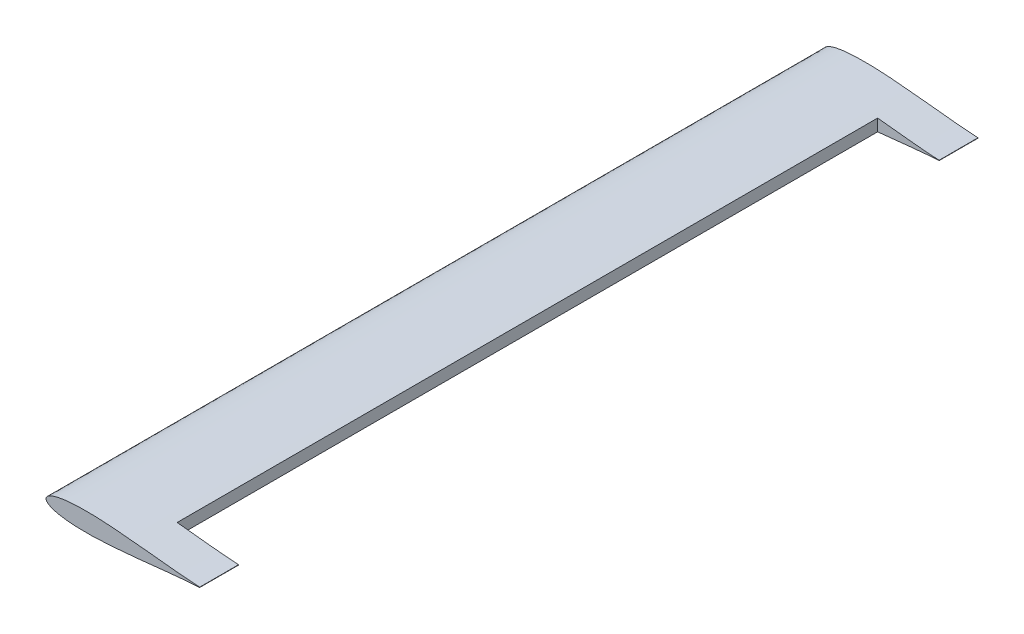
SolidWorks part; units mm, degrees
other "Markup1"
sketch "Sketch3" plane through (-0.0553, -7.355, 609.6) normal (0, 0, 1) x (1, 0, 0)
ref_plane "Front Plane" through (0, 0, 0) normal (0, 0, 1) x (1, 0, 0)
ref_plane "Top Plane" through (0, 0, 0) normal (0, 1, 0) x (1, 0, 0)
ref_plane "Right Plane" through (0, 0, 0) normal (1, 0, 0) x (0, 0, -1)
curve "Curve1"
  spline degree 3 poles (25.3337, -0.0003, 0) (25.4166, 0, 0) (25.3337, 0.0003, 0) (25.2654, 0.0018, 0) (25.098, 0.0055, 0) (24.8899, 0.0127, 0) (24.614, 0.0243, 0) (24.2833, 0.0411, 0) (23.8951, 0.064, 0) (23.4526, 0.0935, 0) (22.9577, 0.1302, 0) (22.4128, 0.1742, 0) (21.8206, 0.2257, 0) (21.184, 0.2845, 0) (20.5061, 0.3502, 0) (19.7901, 0.4224, 0) (19.0396, 0.5004, 0) (18.2582, 0.5832, 0) (17.4498, 0.6697, 0) (16.6182, 0.7589, 0) (15.7675, 0.8494, 0) (14.9019, 0.9396, 0) (14.0255, 1.0282, 0) (13.1427, 1.1135, 0) (12.2578, 1.1941, 0) (11.3749, 1.2683, 0) (10.4986, 1.3345, 0) (9.6329, 1.3915, 0) (8.7821, 1.4377, 0) (7.9504, 1.4721, 0) (7.1418, 1.4935, 0) (6.3603, 1.501, 0) (5.6096, 1.4941, 0) (4.8934, 1.4721, 0) (4.2152, 1.4349, 0) (3.5783, 1.3824, 0) (2.9857, 1.3149, 0) (2.4403, 1.233, 0) (1.9447, 1.1371, 0) (1.5013, 1.0283, 0) (1.1121, 0.9078, 0) (0.7787, 0.7769, 0) (0.5025, 0.6369, 0) (0.2843, 0.4891, 0) (0.1244, 0.334, 0) (0.024, 0.1711, 0) (-0.0113, 0, 0) (0.024, -0.1711, 0) (0.1244, -0.334, 0) (0.2843, -0.4891, 0) (0.5025, -0.6369, 0) (0.7787, -0.7769, 0) (1.1121, -0.9078, 0) (1.5013, -1.0283, 0) (1.9447, -1.1371, 0) (2.4403, -1.233, 0) (2.9857, -1.3149, 0) (3.5783, -1.3824, 0) (4.2152, -1.4349, 0) (4.8934, -1.4721, 0) (5.6096, -1.4941, 0) (6.3603, -1.501, 0) (7.1418, -1.4935, 0) (7.9504, -1.4721, 0) (8.7821, -1.4377, 0) (9.6329, -1.3915, 0) (10.4986, -1.3345, 0) (11.3749, -1.2683, 0) (12.2578, -1.1941, 0) (13.1427, -1.1135, 0) (14.0255, -1.0282, 0) (14.9019, -0.9396, 0) (15.7675, -0.8494, 0) (16.6182, -0.7589, 0) (17.4498, -0.6697, 0) (18.2582, -0.5832, 0) (19.0396, -0.5004, 0) (19.7901, -0.4224, 0) (20.5061, -0.3502, 0) (21.184, -0.2845, 0) (21.8206, -0.2257, 0) (22.4128, -0.1742, 0) (22.9577, -0.1302, 0) (23.4526, -0.0935, 0) (23.8951, -0.064, 0) (24.2833, -0.0411, 0) (24.614, -0.0243, 0) (24.8899, -0.0127, 0) (25.098, -0.0055, 0) (25.2654, -0.0018, 0) (25.3337, -0.0003, 0) (25.4166, 0, 0) (25.3337, 0.0003, 0) knots -0.005355 -0.002385 -0.000597 0 0.000597 0.002385 0.005355 0.009495 0.014784 0.021198 0.028708 0.037278 0.046868 0.05743 0.068917 0.081271 0.094432 0.108338 0.122919 0.138103 0.153815 0.169978 0.186509 0.203327 0.220349 0.237488 0.25466 0.271779 0.288763 0.305527 0.32199 0.338073 0.353702 0.368803 0.383306 0.397149 0.410269 0.422614 0.434133 0.444783 0.454527 0.463337 0.471194 0.478092 0.484042 0.489082 0.493295 0.496842 0.5 0.503158 0.506705 0.510918 0.515958 0.521908 0.528806 0.536663 0.545473 0.555218 0.565867 0.577386 0.589731 0.602851 0.616694 0.631197 0.646298 0.661927 0.67801 0.694473 0.711237 0.728221 0.74534 0.762512 0.779651 0.796673 0.813491 0.830023 0.846185 0.861897 0.877081 0.891662 0.905568 0.918729 0.931083 0.94257 0.953133 0.962722 0.971292 0.978802 0.985216 0.990505 0.994645 0.997615 0.999403 1 1.000597 1.002385 1.005355 periodic
sketch "Sketch2" plane through (0, 0, 0) normal (0, 0, 1) x (1, 0, 0)
  line L0 (0, 0) -> (25.4, 0) construction
  line L1 (0, 0) -> (124.46, 0) construction
  line L2 (120.381, 0.1319) -> (120.381, -0.1319)
  line L3 (62.23, 0) -> (62.23, 5.6527) construction
  spline S0 degree 3 poles (25.3337, -0.0003) (25.4166, 0) (25.3337, 0.0003) (25.2654, 0.0018) (25.098, 0.0055) (24.8899, 0.0127) (24.614, 0.0243) (24.2833, 0.0411) (23.8951, 0.064) (23.4526, 0.0935) (22.9577, 0.1302) (22.4128, 0.1742) (21.8206, 0.2257) (21.184, 0.2845) (20.5061, 0.3502) (19.7901, 0.4224) (19.0396, 0.5004) (18.2582, 0.5832) (17.4498, 0.6697) (16.6182, 0.7589) (15.7675, 0.8494) (14.9019, 0.9396) (14.0255, 1.0282) (13.1427, 1.1135) (12.2578, 1.1941) (11.3749, 1.2683) (10.4986, 1.3345) (9.6329, 1.3915) (8.7821, 1.4377) (7.9504, 1.4721) (7.1418, 1.4935) (6.3603, 1.501) (5.6096, 1.4941) (4.8934, 1.4721) (4.2152, 1.4349) (3.5783, 1.3824) (2.9857, 1.3149) (2.4403, 1.233) (1.9447, 1.1371) (1.5013, 1.0283) (1.1121, 0.9078) (0.7787, 0.7769) (0.5025, 0.6369) (0.2843, 0.4891) (0.1244, 0.334) (0.024, 0.1711) (-0.0113, 0) (0.024, -0.1711) (0.1244, -0.334) (0.2843, -0.4891) (0.5025, -0.6369) (0.7787, -0.7769) (1.1121, -0.9078) (1.5013, -1.0283) (1.9447, -1.1371) (2.4403, -1.233) (2.9857, -1.3149) (3.5783, -1.3824) (4.2152, -1.4349) (4.8934, -1.4721) (5.6096, -1.4941) (6.3603, -1.501) (7.1418, -1.4935) (7.9504, -1.4721) (8.7821, -1.4377) (9.6329, -1.3915) (10.4986, -1.3345) (11.3749, -1.2683) (12.2578, -1.1941) (13.1427, -1.1135) (14.0255, -1.0282) (14.9019, -0.9396) (15.7675, -0.8494) (16.6182, -0.7589) (17.4498, -0.6697) (18.2582, -0.5832) (19.0396, -0.5004) (19.7901, -0.4224) (20.5061, -0.3502) (21.184, -0.2845) (21.8206, -0.2257) (22.4128, -0.1742) (22.9577, -0.1302) (23.4526, -0.0935) (23.8951, -0.064) (24.2833, -0.0411) (24.614, -0.0243) (24.8899, -0.0127) (25.098, -0.0055) (25.2654, -0.0018) (25.3337, -0.0003) (25.4166, 0) (25.3337, 0.0003) knots -0.005355 -0.002385 -0.000597 0 0.000597 0.002385 0.005355 0.009495 0.014784 0.021198 0.028708 0.037278 0.046868 0.05743 0.068917 0.081271 0.094432 0.108338 0.122919 0.138103 0.153815 0.169978 0.186509 0.203327 0.220349 0.237488 0.25466 0.271779 0.288763 0.305527 0.32199 0.338073 0.353702 0.368803 0.383306 0.397149 0.410269 0.422614 0.434133 0.444783 0.454527 0.463337 0.471194 0.478092 0.484042 0.489082 0.493295 0.496842 0.5 0.503158 0.506705 0.510918 0.515958 0.521908 0.528806 0.536663 0.545473 0.555218 0.565867 0.577386 0.589731 0.602851 0.616694 0.631197 0.646298 0.661927 0.67801 0.694473 0.711237 0.728221 0.74534 0.762512 0.779651 0.796673 0.813491 0.830023 0.846185 0.861897 0.877081 0.891662 0.905568 0.918729 0.931083 0.94257 0.953133 0.962722 0.971292 0.978802 0.985216 0.990505 0.994645 0.997615 0.999403 1 1.000597 1.002385 1.005355 only from (25.4, 0) to (25.4, 0) construction
  spline S1 degree 3 poles (25.3337, -0.0003) (25.4166, 0) (25.3337, 0.0003) (25.2654, 0.0018) (25.098, 0.0055) (24.8899, 0.0127) (24.614, 0.0243) (24.2833, 0.0411) (23.8951, 0.064) (23.4526, 0.0935) (22.9577, 0.1302) (22.4128, 0.1742) (21.8206, 0.2257) (21.184, 0.2845) (20.5061, 0.3502) (19.7901, 0.4224) (19.0396, 0.5004) (18.2582, 0.5832) (17.4498, 0.6697) (16.6182, 0.7589) (15.7675, 0.8494) (14.9019, 0.9396) (14.0255, 1.0282) (13.1427, 1.1135) (12.2578, 1.1941) (11.3749, 1.2683) (10.4986, 1.3345) (9.6329, 1.3915) (8.7821, 1.4377) (7.9504, 1.4721) (7.1418, 1.4935) (6.3603, 1.501) (5.6096, 1.4941) (4.8934, 1.4721) (4.2152, 1.4349) (3.5783, 1.3824) (2.9857, 1.3149) (2.4403, 1.233) (1.9447, 1.1371) (1.5013, 1.0283) (1.1121, 0.9078) (0.7787, 0.7769) (0.5025, 0.6369) (0.2843, 0.4891) (0.1244, 0.334) (0.024, 0.1711) (-0.0113, 0) (0.024, -0.1711) (0.1244, -0.334) (0.2843, -0.4891) (0.5025, -0.6369) (0.7787, -0.7769) (1.1121, -0.9078) (1.5013, -1.0283) (1.9447, -1.1371) (2.4403, -1.233) (2.9857, -1.3149) (3.5783, -1.3824) (4.2152, -1.4349) (4.8934, -1.4721) (5.6096, -1.4941) (6.3603, -1.501) (7.1418, -1.4935) (7.9504, -1.4721) (8.7821, -1.4377) (9.6329, -1.3915) (10.4986, -1.3345) (11.3749, -1.2683) (12.2578, -1.1941) (13.1427, -1.1135) (14.0255, -1.0282) (14.9019, -0.9396) (15.7675, -0.8494) (16.6182, -0.7589) (17.4498, -0.6697) (18.2582, -0.5832) (19.0396, -0.5004) (19.7901, -0.4224) (20.5061, -0.3502) (21.184, -0.2845) (21.8206, -0.2257) (22.4128, -0.1742) (22.9577, -0.1302) (23.4526, -0.0935) (23.8951, -0.064) (24.2833, -0.0411) (24.614, -0.0243) (24.8899, -0.0127) (25.098, -0.0055) (25.2654, -0.0018) (25.3337, -0.0003) (25.4166, 0) (25.3337, 0.0003) knots -0.005355 -0.002385 -0.000597 0 0.000597 0.002385 0.005355 0.009495 0.014784 0.021198 0.028708 0.037278 0.046868 0.05743 0.068917 0.081271 0.094432 0.108338 0.122919 0.138103 0.153815 0.169978 0.186509 0.203327 0.220349 0.237488 0.25466 0.271779 0.288763 0.305527 0.32199 0.338073 0.353702 0.368803 0.383306 0.397149 0.410269 0.422614 0.434133 0.444783 0.454527 0.463337 0.471194 0.478092 0.484042 0.489082 0.493295 0.496842 0.5 0.503158 0.506705 0.510918 0.515958 0.521908 0.528806 0.536663 0.545473 0.555218 0.565867 0.577386 0.589731 0.602851 0.616694 0.631197 0.646298 0.661927 0.67801 0.694473 0.711237 0.728221 0.74534 0.762512 0.779651 0.796673 0.813491 0.830023 0.846185 0.861897 0.877081 0.891662 0.905568 0.918729 0.931083 0.94257 0.953133 0.962722 0.971292 0.978802 0.985216 0.990505 0.994645 0.997615 0.999403 1 1.000597 1.002385 1.005355 only from (25.4, 0) to (25.4, 0) construction
  spline S2 degree 3 poles (120.381, 0.1319) (119.9463, 0.1527) (118.8798, 0.2078) (117.0858, 0.3137) (114.9178, 0.4584) (112.4927, 0.6382) (109.8228, 0.8537) (106.9211, 1.106) (103.8017, 1.394) (100.4797, 1.7159) (96.9715, 2.0698) (93.294, 2.4518) (89.4653, 2.8575) (85.5038, 3.2818) (81.4291, 3.7187) (77.2608, 4.162) (73.0193, 4.6041) (68.7252, 5.0383) (64.3994, 5.4564) (60.0631, 5.8512) (55.7372, 6.2145) (51.4429, 6.5392) (47.2011, 6.8181) (43.0324, 7.0448) (38.9571, 7.2131) (34.9951, 7.3181) (31.1655, 7.355) (27.4872, 7.3209) (23.9779, 7.2133) (20.6546, 7.0309) (17.5336, 6.7739) (14.6298, 6.4432) (11.9574, 6.0415) (9.5291, 5.5718) (7.3563, 5.0389) (5.4492, 4.4484) (3.8158, 3.8067) (2.4624, 3.1207) (1.3928, 2.3964) (0.6096, 1.6368) (0.1174, 0.8384) (-0.0553, 0) (0.1174, -0.8384) (0.6096, -1.6368) (1.3928, -2.3964) (2.4624, -3.1207) (3.8158, -3.8067) (5.4492, -4.4484) (7.3563, -5.0389) (9.5291, -5.5718) (11.9574, -6.0415) (14.6299, -6.4433) (17.5336, -6.7739) (20.6546, -7.0309) (23.9779, -7.2133) (27.4872, -7.3209) (31.1655, -7.355) (34.9951, -7.3181) (38.9571, -7.2131) (43.0324, -7.0448) (47.2011, -6.8181) (51.4429, -6.5392) (55.7372, -6.2145) (60.0631, -5.8512) (64.3994, -5.4564) (68.7252, -5.0383) (73.0193, -4.6041) (77.2608, -4.162) (81.4291, -3.7187) (85.5039, -3.2817) (89.4653, -2.8575) (93.294, -2.4518) (96.9715, -2.0698) (100.4797, -1.7159) (103.8017, -1.394) (106.9211, -1.106) (109.8228, -0.8537) (112.4927, -0.6382) (114.9179, -0.4584) (117.0858, -0.3137) (118.8798, -0.2078) (119.9463, -0.1527) (120.381, -0.1319) knots 0.016066 0.016066 0.016066 0.016066 0.021198 0.028708 0.037278 0.046868 0.05743 0.068917 0.081271 0.094432 0.108338 0.122919 0.138103 0.153815 0.169978 0.186509 0.203327 0.220349 0.237488 0.25466 0.271779 0.288763 0.305527 0.32199 0.338073 0.353702 0.368803 0.383306 0.397149 0.410269 0.422614 0.434133 0.444783 0.454527 0.463337 0.471194 0.478092 0.484042 0.489082 0.493295 0.496842 0.5 0.503158 0.506705 0.510918 0.515958 0.521908 0.528806 0.536663 0.545473 0.555218 0.565867 0.577386 0.589731 0.602851 0.616694 0.631197 0.646298 0.661927 0.67801 0.694473 0.711237 0.728221 0.74534 0.762512 0.779651 0.796673 0.813491 0.830023 0.846185 0.861897 0.877081 0.891662 0.905568 0.918729 0.931083 0.94257 0.953133 0.962722 0.971292 0.978802 0.983934 0.983934 0.983934 0.983934
  point P8 (0, 0)
  dimension "D1" = 124.46
  dimension "D2" = 4.079
  dimension "D3" = 5.6527
extrude "Boss-Extrude4" add sketch "Sketch2" along normal blind 609.6
sketch "Sketch4" plane through (0, 0, 0) normal (0, 1, 0) x (1, 0, 0)
  line L0 (0, 0) -> (0, -609.6) construction
  line L1 (0, -304.8) -> (120.381, -304.8) construction
  line L2 (120.381, -609.6) -> (120.381, 0) construction
  line L3 (120.381, -304.8) -> (72.2327, -304.8)
  line L4 (72.2327, -579.12) -> (72.2327, -30.48)
  line L5 (72.2327, -30.48) -> (171.5692, -30.48)
  line L6 (171.5692, -30.48) -> (171.5692, -579.12)
  line L7 (171.5692, -579.12) -> (72.2327, -579.12)
  point P12 (72.2327, -304.8)
  dimension "D1" = 48.1482
  dimension "D2" = 548.64
extrude "Cut-Extrude1" cut sketch "Sketch4" against normal through all both and the other way through all
sketch "Sketch5" plane through (0, 0, 30.48) normal (0, 0, 1) x (1, 0, 0)
  line L0 (72.2327, 4.6824) -> (72.2327, -4.6824)
  line L1 (72.2327, 0) -> (120.381, 0) construction
  line L2 (120.381, -0.1319) -> (120.381, 0.1319) construction
  circle A0 centre (76.3067, 0) radius 4.0739 construction
  dimension "D1" = 8.1479
